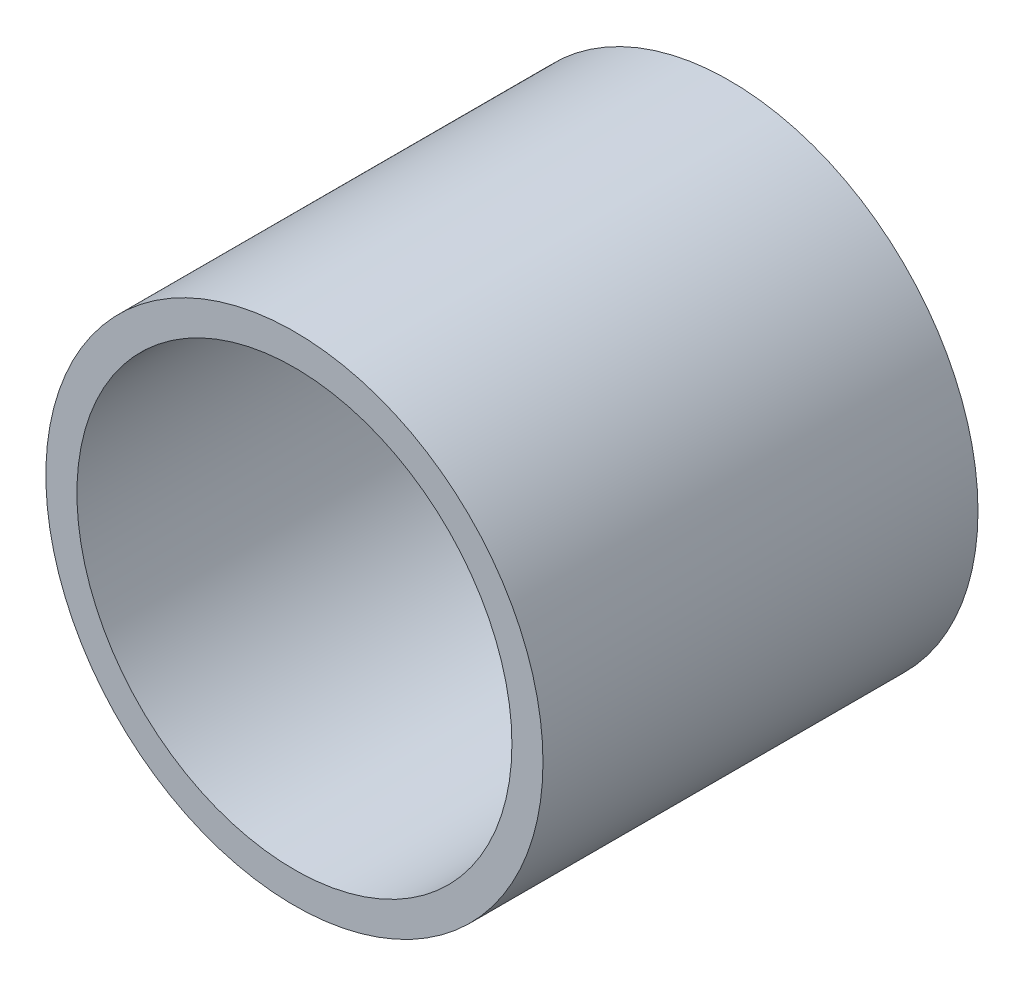
SolidWorks part; units mm, degrees
ref_plane "Front Plane" through (0, 0, 0) normal (0, 0, 1) x (1, 0, 0)
ref_plane "Top Plane" through (0, 0, 0) normal (0, 1, 0) x (1, 0, 0)
ref_plane "Right Plane" through (0, 0, 0) normal (1, 0, 0) x (0, 0, -1)
sketch "Sketch1" plane through (0, 0, 0) normal (0, 0, 1) x (1, 0, 0)
  circle A0 centre (0, 0) radius 6.35
  circle A1 centre (0, 0) radius 5.5562
  dimension "D1" = 0.7937
extrude "Boss-Extrude1" add sketch "Sketch1" along normal blind 11.1125
